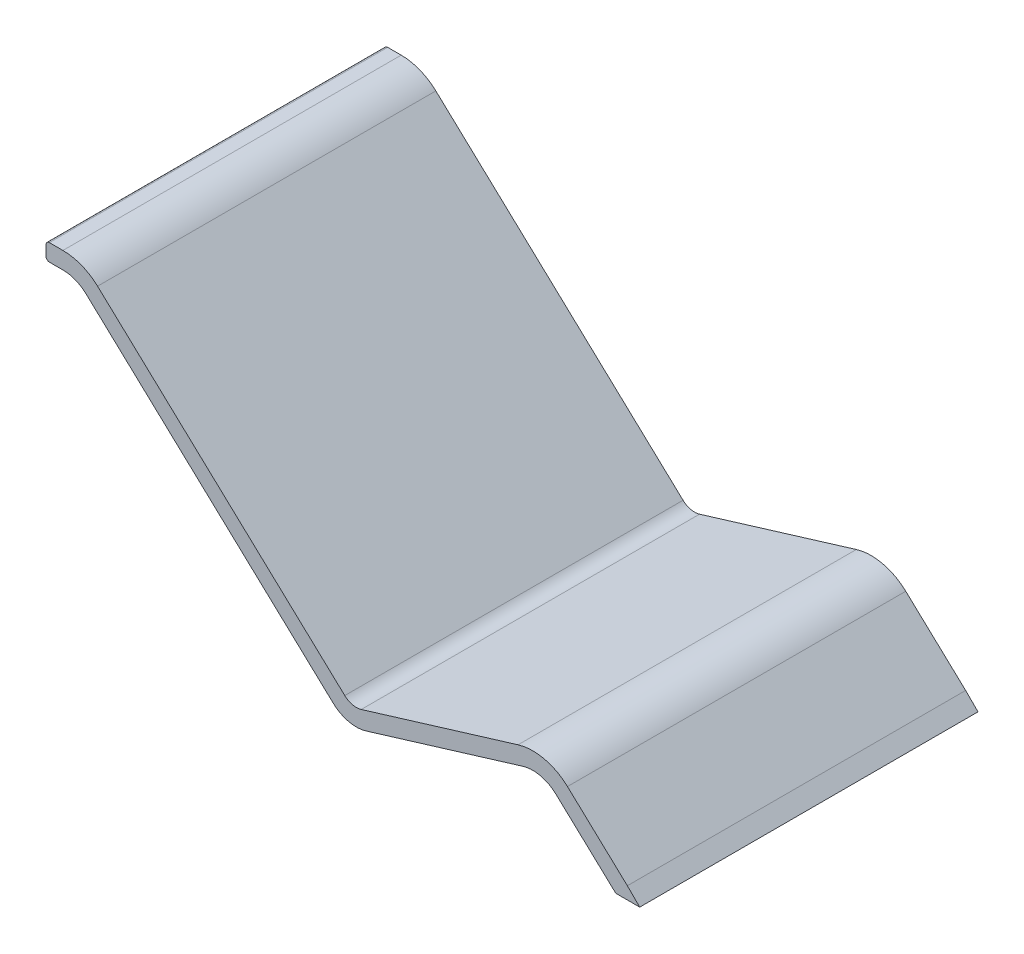
SolidWorks part; units mm, degrees
ref_plane "Front" through (0, 0, 0) normal (0, 0, 1) x (1, 0, 0)
ref_plane "Top" through (0, 0, 0) normal (0, 1, 0) x (1, 0, 0)
ref_plane "Right" through (0, 0, 0) normal (1, 0, 0) x (0, 0, -1)
sketch "草图1" plane through (0, 0, 0) normal (0, 0, 1) x (1, 0, 0)
  line L0 (-4.2195, 3.9407) -> (-77.3033, 72.1958)
  line L1 (5.5225, 1.6838) -> (51.869, 15.8151)
  line L2 (61.611, 13.5582) -> (79.3167, -2.9776)
  line L3 (-84.1288, 74.8874) -> (-88.1288, 74.8874)
  line L4 (-920.6833, -2.9776) -> (86.3836, -2.9776) construction
  line L5 (65.0238, 17.2124) -> (82.7294, 0.6766)
  line L6 (4.0643, 6.4665) -> (50.4108, 20.5977)
  line L7 (-0.8067, 7.5949) -> (-73.8906, 75.85)
  line L8 (-84.1288, 79.8874) -> (-88.1288, 79.8874)
  line L9 (-89.1288, 78.8874) -> (-89.1288, 75.8874)
  line L10 (82.7294, 0.6766) -> (86.3836, -2.9776)
  line L11 (79.3167, -2.9776) -> (86.3836, -2.9776)
  line L12 (88.2732, -2.9776) -> (49079.3167, -2.9776) construction
  line L13 (-84.1288, 74.8874) -> (-89.1288, 74.8874) construction
  line L14 (-84.1288, 79.8874) -> (-89.1288, 79.8874) construction
  arc A0 (-77.3033, 72.1958) -> (-84.1288, 74.8874) centre (-84.1288, 64.8874) ccw
  arc A1 (61.611, 13.5582) -> (51.869, 15.8151) centre (54.7855, 6.2499) ccw
  arc A2 (5.5225, 1.6838) -> (-4.2195, 3.9407) centre (2.606, 11.2491) cw
  arc A3 (65.0238, 17.2124) -> (50.4108, 20.5977) centre (54.7855, 6.2499) ccw
  arc A4 (4.0643, 6.4665) -> (-0.8067, 7.5949) centre (2.606, 11.2491) cw
  arc A5 (-73.8906, 75.85) -> (-84.1288, 79.8874) centre (-84.1288, 64.8874) ccw
  arc A6 (-88.1288, 74.8874) -> (-89.1288, 75.8874) centre (-88.1288, 75.8874) cw
  arc A7 (-88.1288, 79.8874) -> (-89.1288, 78.8874) centre (-88.1288, 78.8874) ccw
  point P10 (57.3915, 17.4989)
  point P13 (0, 0)
  point P32 (-89.1288, 74.8874)
  dimension "D1" = 10
  dimension "D6" = 10
  dimension "D8" = 100
  dimension "D10" = 1
  dimension "D2" = 120
  dimension "D3" = 60
  dimension "D4" = 30
  dimension "D5" = 120
  dimension "D7" = 5
  dimension "D9" = 5
extrude "凸台-拉伸1" add sketch "草图1" along normal blind 100
sketch "草图2" plane through (0, 0, 100) normal (0, 0, 1) x (1, 0, 0)
  line L0 (-16.9414, 22.6635) -> (-82.9217, -2.9776)
  line L1 (-23.3621, 21.8925) -> (5.0737, 21.8925)
  line L2 (-23.3621, 21.8925) -> (-23.3621, 26.2368)
  line L3 (-23.3621, 26.2368) -> (5.0737, 26.2368)
  line L4 (5.0737, 21.8925) -> (5.0737, 26.2368)
  line L5 (-16.9414, 22.6635) -> (-7.1798, 22.6635)
  line L6 (-82.9217, -2.9776) -> (-73.1601, -2.9776)
  line L7 (-7.1798, 22.6635) -> (-73.1601, -2.9776)
  line L8 (-0.8067, 7.5949) -> (-73.8906, 75.85) construction
